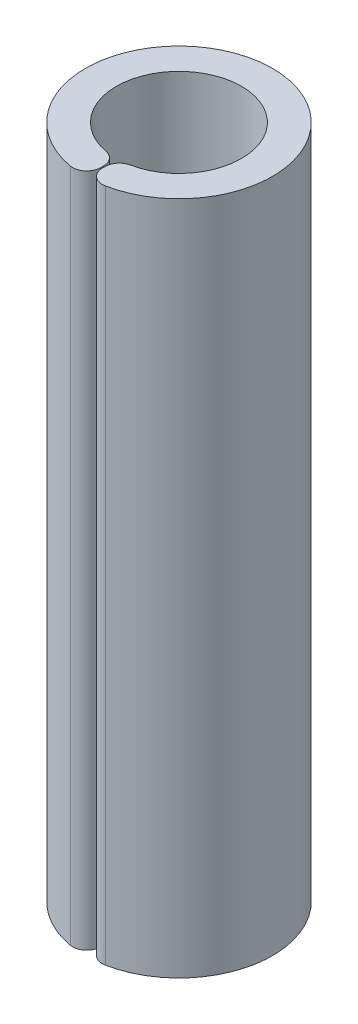
SolidWorks part; units mm, degrees
ref_plane "Front" through (0, 0, 0) normal (0, 0, 1) x (1, 0, 0)
ref_plane "Top" through (0, 0, 0) normal (0, 1, 0) x (1, 0, 0)
ref_plane "Right" through (0, 0, 0) normal (1, 0, 0) x (0, 0, -1)
sketch "Sketch1" plane through (0, 0, 0) normal (0, 1, 0) x (1, 0, 0)
  line L0 (0, 0) -> (0, -4) construction
  line L1 (0, 0) -> (0.0698, -3.9994) construction
  line L2 (0.0467, -2.6746) -> (0.0698, -3.9994)
  line L3 (0, -2.675) -> (0, -4)
  circle A0 centre (0, 0) radius 4 construction
  circle A1 centre (0, 0) radius 2.675 construction
  arc A2 (0.0467, -2.6746) -> (0, -2.675) centre (0, 0) ccw
  arc A3 (0.0698, -3.9994) -> (0, -4) centre (0, 0) ccw
  dimension "D1" = 5.35
  dimension "D2" = 8
  dimension "D3" = 1
extrude "Boss-Extrude1" add sketch "Sketch1" along normal blind 28.85
fillet "Fillet1" radius 0.6 4 edges at (0.0698, 14.425, 3.9994) (0, 14.425, 4) (0.0467, 14.425, 2.6746) (0, 14.425, 2.675)
